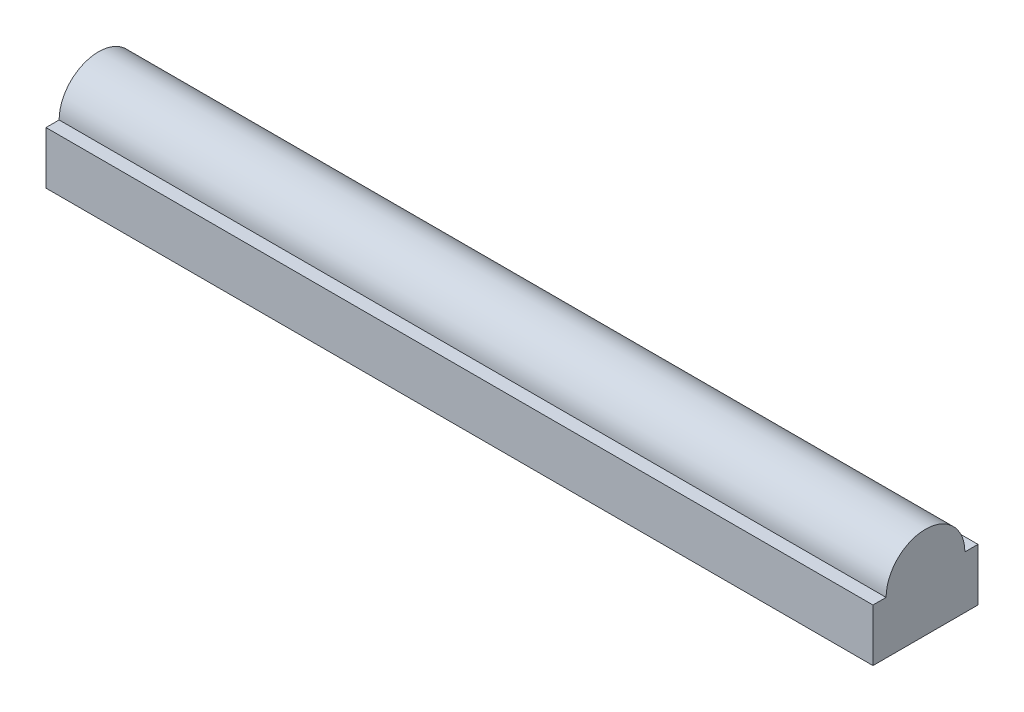
SolidWorks part; units mm, degrees
ref_plane "Front Plane" through (0, 0, 0) normal (0, 0, 1) x (1, 0, 0)
ref_plane "Top Plane" through (0, 0, 0) normal (0, 1, 0) x (1, 0, 0)
ref_plane "Right Plane" through (0, 0, 0) normal (1, 0, 0) x (0, 0, -1)
sketch "Sketch1" plane through (0, 0, 0) normal (1, 0, 0) x (0, 0, -1)
  line L0 (0, 0) -> (50.8, 0)
  line L1 (50.8, 0) -> (50.8, 25.4)
  line L2 (50.8, 25.4) -> (44.45, 25.4)
  line L3 (0, 25.4) -> (0, 0)
  line L4 (6.35, 25.4) -> (0, 25.4)
  arc A0 (44.45, 25.4) -> (6.35, 25.4) centre (25.4, 25.4) ccw
  dimension "D3" = 38.1
  dimension "D4" = 25.4
  dimension "D1" = 25.4
  dimension "D2" = 50.8
extrude "Boss-Extrude1" add sketch "Sketch1" along normal blind 400
